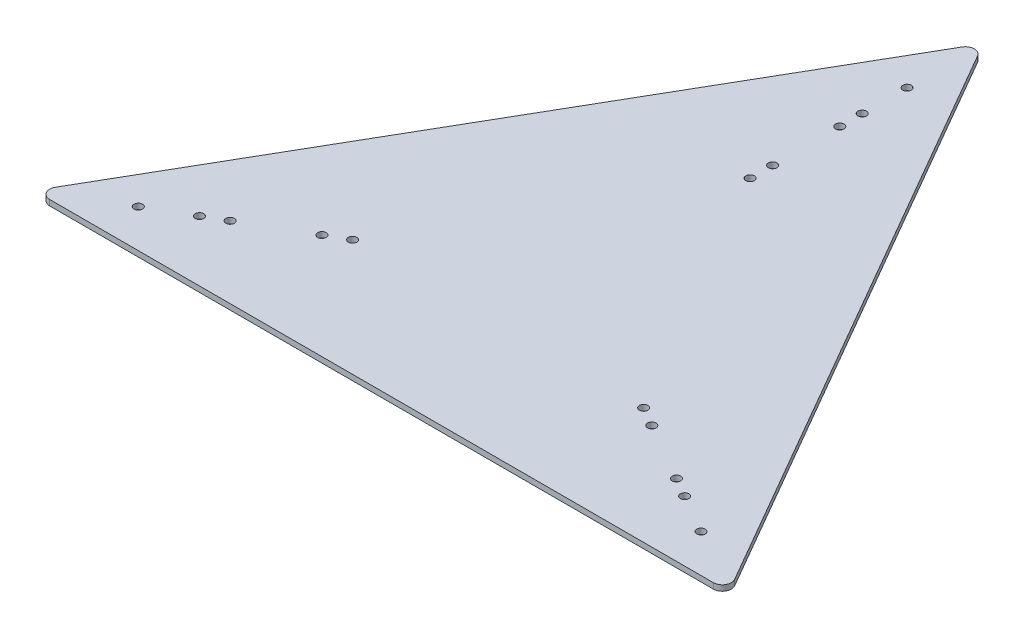
SolidWorks part; units mm, degrees
ref_plane "Front Plane" through (0, 0, 0) normal (0, 0, 1) x (1, 0, 0)
ref_plane "Top Plane" through (0, 0, 0) normal (0, 1, 0) x (1, 0, 0)
ref_plane "Right Plane" through (0, 0, 0) normal (1, 0, 0) x (0, 0, -1)
sketch "Sketch1" plane through (0, 0, 0) normal (0, 1, 0) x (1, 0, 0)
  line L0 (0, 0) -> (393.7, 0)
  line L1 (393.7, 0) -> (196.85, 340.9542)
  line L2 (196.85, 340.9542) -> (0, 0)
  dimension "D1" = 393.7
extrude "Boss-Extrude1" add sketch "Sketch1" along normal blind 3.175
fillet "Fillet1" radius 5.08 3 edges at (196.85, 1.5875, -340.9542) (393.7, 1.5875, 0) (0, 1.5875, 0)
sketch "Sketch2" plane through (0, 3.175, 0) normal (0, 1, 0) x (1, 0, 0)
  line L0 (4.3994, 2.54) -> (295.275, 170.4771) construction
  line L1 (389.3006, 7.62) -> (201.2494, 333.3342) construction
  line L2 (389.3006, 2.54) -> (98.425, 170.4771) construction
  line L3 (192.4506, 333.3342) -> (4.3994, 7.62) construction
  line L4 (196.85, 335.8742) -> (196.85, 0) construction
  line L5 (8.7988, 0) -> (384.9012, 0) construction
  arc A0 (4.3994, 7.62) -> (8.7988, 0) centre (8.7988, 5.08) ccw construction
  arc A1 (384.9012, 0) -> (389.3006, 7.62) centre (384.9012, 5.08) ccw construction
  arc A2 (201.2494, 333.3342) -> (192.4506, 333.3342) centre (196.85, 330.7942) ccw construction
  circle A8 centre (37.395, 21.59) radius 2.413
  circle A10 centre (59.392, 34.29) radius 2.413
  circle A11 centre (70.3905, 40.64) radius 2.413
  circle A13 centre (114.3846, 66.04) radius 2.413
  circle A14 centre (103.3861, 59.69) radius 2.413
  circle A17 centre (196.85, 297.7742) radius 2.413
  circle A19 centre (196.85, 272.3742) radius 2.413
  circle A20 centre (196.85, 259.6742) radius 2.413
  circle A23 centre (196.85, 221.5742) radius 2.413
  circle A24 centre (196.85, 208.8742) radius 2.413
  circle A25 centre (279.3154, 66.04) radius 2.413
  circle A26 centre (290.3139, 59.69) radius 2.413
  circle A29 centre (323.3095, 40.64) radius 2.413
  circle A30 centre (334.308, 34.29) radius 2.413
  circle A32 centre (356.305, 21.59) radius 2.413
  dimension "D3" = 4.826
  dimension "D8" = 25.4
  dimension "D2" = 38.1
  dimension "D4" = 25.4
  dimension "D5" = 38.1
  dimension "D6" = 12.7
  dimension "D7" = 38.1
  dimension "D9" = 12.7
  dimension "D10" = 12.7
  dimension "D11" = 38.1
  dimension "D12" = 12.7
extrude "Cut-Extrude1" cut sketch "Sketch2" against normal up to surface (14.1535 mm away)
sketch "Sketch3" plane through (0, 3.175, 0) normal (0, 1, 0) x (1, 0, 0)
  line L2 (-21.1478, 374.9145) -> (410.6522, 374.9145)
  line L3 (-21.1478, 374.9145) -> (-21.1478, -56.8855)
  line L4 (-21.1478, -56.8855) -> (410.6522, -56.8855)
  line L5 (410.6522, 374.9145) -> (410.6522, -56.8855)
  dimension "D1" = 431.8
sketch "Sketch4" plane through (0, 3.175, 0) normal (0, 1, 0) x (1, 0, 0)
  line L0 (196.85, 0) -> (196.85, 335.8742)
  line L1 (8.7988, 0) -> (384.9012, 0) construction
  arc A0 (201.2494, 333.3342) -> (192.4506, 333.3342) centre (196.85, 330.7942) ccw construction
  dimension "D1" = 335.8742
